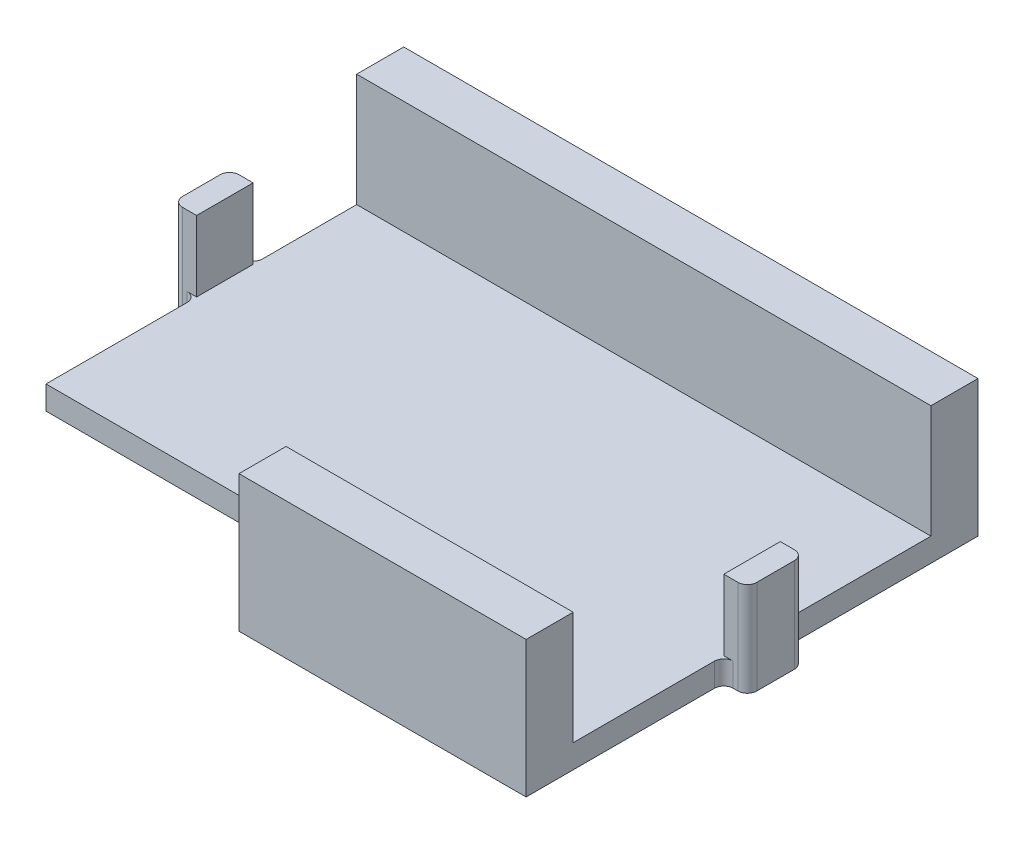
SolidWorks part; units mm, degrees
ref_plane "Front Plane" through (0, 0, 0) normal (0, 0, 1) x (1, 0, 0)
ref_plane "Top Plane" through (0, 0, 0) normal (0, 1, 0) x (1, 0, 0)
ref_plane "Right Plane" through (0, 0, 0) normal (1, 0, 0) x (0, 0, -1)
sketch "Sketch1" plane through (0, 0, 0) normal (0, 1, 0) x (1, 0, 0)
  line L0 (0, 10) -> (30.5, 10)
  line L3 (0, 48) -> (61, 48)
  line L4 (61, 0) -> (61, 48)
  line L5 (30.5, 10) -> (30.5, 0)
  line L6 (0, 48) -> (0, 10)
  line L7 (30.5, 0) -> (61, 0)
  dimension "D1" = 61
  dimension "D2" = 48
  dimension "D3" = 30.5
  dimension "D4" = 10
extrude "Boss-Extrude1" add sketch "Sketch1" along normal blind 2.5
sketch "Sketch2" plane through (0, 2.5, 0) normal (0, 1, 0) x (1, 0, 0)
  line L24 (61, 0) -> (61, 48) construction
  line L25 (0, 48) -> (61, 48)
  line L26 (0, 48) -> (0, 43)
  line L27 (0, 43) -> (61, 43)
  line L28 (61, 48) -> (61, 43)
  line L30 (30.5, 0) -> (61, 0)
  line L31 (30.5, 0) -> (30.5, 5)
  line L32 (30.5, 5) -> (61, 5)
  line L33 (61, 0) -> (61, 5)
  dimension "D1" = 5
  dimension "D2" = 5
extrude "Boss-Extrude2" add sketch "Sketch2" along normal blind 12
sketch "Sketch3" plane through (0, 0, 0) normal (0, -1, 0) x (1, 0, 0)
  line L0 (61, -24) -> (0, -24) construction
  line L1 (61, 0) -> (61, -48) construction
  line L2 (0, -48) -> (0, -10) construction
  text T0 "PCB" font "Arial Rounded MT Bold" height 8
extrude "Cut-Extrude1" cut sketch "Sketch3" against normal blind 1
sketch "Sketch5" plane through (0, 0, 0) normal (0, -1, 0) x (1, 0, 0)
  line L0 (0, -29) -> (61, -29) construction
  line L1 (0, -48) -> (0, -10) construction
  line L2 (61, 0) -> (61, -48) construction
  line L3 (0, -26) -> (61, -26) construction
  line L4 (0, -32) -> (61, -32) construction
  line L7 (61, -24) -> (0, -24) construction
  line L8 (61, -21) -> (33.7768, -21) construction
  line L9 (61, -27) -> (35.9613, -27) construction
  line L12 (0, -26) -> (-2.5, -26)
  line L13 (0, -26) -> (0, -32)
  line L14 (0, -32) -> (-2.5, -32)
  line L15 (-2.5, -26) -> (-2.5, -32)
  line L16 (61, -21) -> (63.5, -21)
  line L17 (61, -21) -> (61, -27)
  line L18 (61, -27) -> (63.5, -27)
  line L19 (63.5, -21) -> (63.5, -27)
  dimension "D1" = 3
  dimension "D2" = 3
  dimension "D3" = 3
  dimension "D4" = 3
  dimension "D5" = 2.5
  dimension "D6" = 2.5
extrude "Boss-Extrude3" add sketch "Sketch5" against normal blind 10
fillet "Fillet4" radius 1 8 edges at (0, 1.25, -26) (0, 1.25, -32) (-2.5, 5, -32) (-2.5, 5, -26) (61, 1.25, -27) (61, 1.25, -21) (63.5, 5, -21) (63.5, 5, -27)
